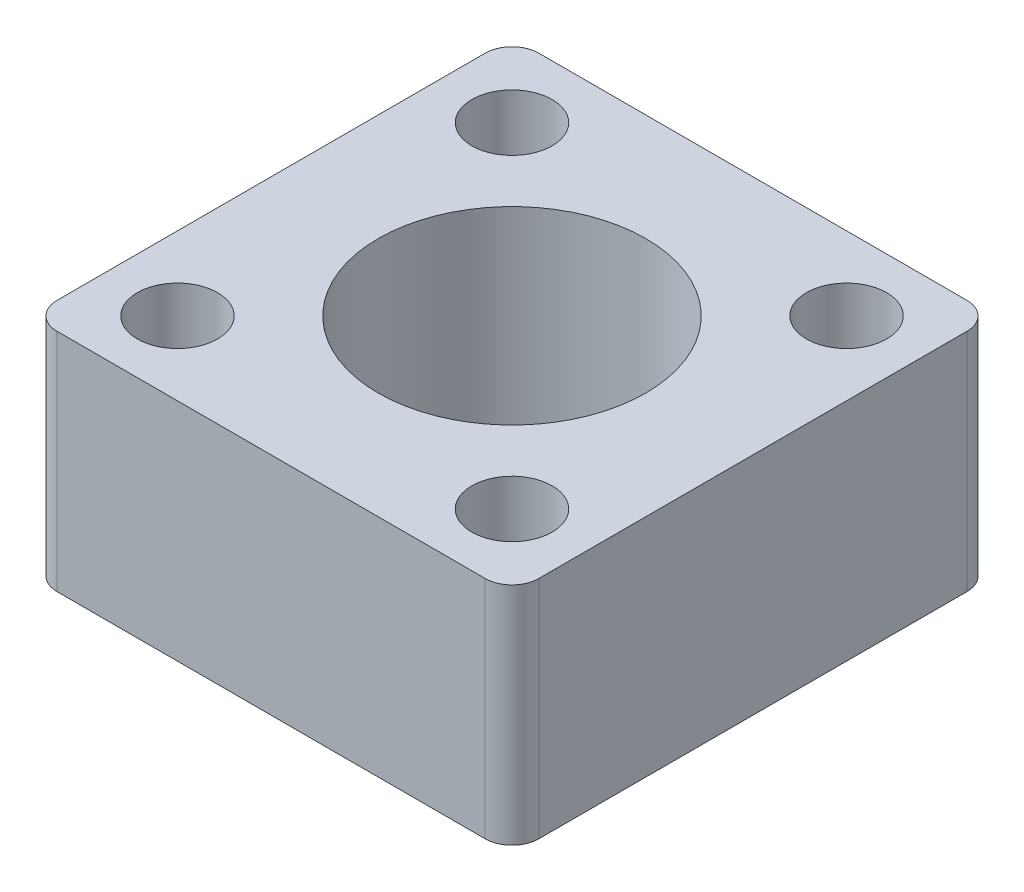
SolidWorks part; units mm, degrees
material "瞎编数据的PLA"
ref_plane "前视基准面" through (0, 0, 0) normal (0, 0, 1) x (1, 0, 0)
ref_plane "上视基准面" through (0, 0, 0) normal (0, 1, 0) x (1, 0, 0)
ref_plane "右视基准面" through (0, 0, 0) normal (1, 0, 0) x (0, 0, -1)
sketch "草图1" plane through (0, 0, 0) normal (0, 0, 1) x (1, 0, 0)
  line L1 (-18, 8.425) -> (18, 8.425)
  line L2 (-18, 8.425) -> (-18, -8.425)
  line L3 (-18, -8.425) -> (18, -8.425)
  line L4 (18, 8.425) -> (18, -8.425)
  line L5 (-18, 8.425) -> (18, -8.425) construction
  line L6 (-18, -8.425) -> (18, 8.425) construction
  point P0 (0, 0)
  dimension "D1" = 16.85
  dimension "D2" = 36
extrude "凸台-拉伸1" add sketch "草图1" along normal blind 36
sketch "草图2" plane through (0, 8.425, 0) normal (0, 1, 0) x (1, 0, 0)
  line L0 (0, 0) -> (0, -36) construction
  line L1 (18, -36) -> (-18, -36) construction
  line L3 (-12.5, -30.5) -> (12.5, -30.5) construction
  line L4 (-12.5, -30.5) -> (-12.5, -5.5) construction
  line L5 (-12.5, -5.5) -> (12.5, -5.5) construction
  line L6 (12.5, -30.5) -> (12.5, -5.5) construction
  line L8 (-12.5, -5.5) -> (12.5, -30.5) construction
  circle A0 centre (-12.5, -5.5) radius 3
  circle A1 centre (-12.5, -30.5) radius 3
  circle A2 centre (12.5, -30.5) radius 3
  circle A3 centre (12.5, -5.5) radius 3
  point P6 (0, -18)
  dimension "D3" = 6
  dimension "D1" = 25
  dimension "D2" = 25
extrude "切除-拉伸1" cut sketch "草图2" against normal through all
sketch "草图3" plane through (0, 8.425, 0) normal (0, 1, 0) x (1, 0, 0)
  line L0 (0, 0) -> (0, -36) construction
  line L1 (18, -36) -> (-18, -36) construction
  circle A0 centre (0, -18) radius 10
  dimension "D1" = 20
extrude "切除-拉伸2" cut sketch "草图3" against normal through all
fillet "圆角1" radius 2 4 edges at (-18, 0, 36) (-18, 0, 0) (18, 0, 0) (18, 0, 36)
